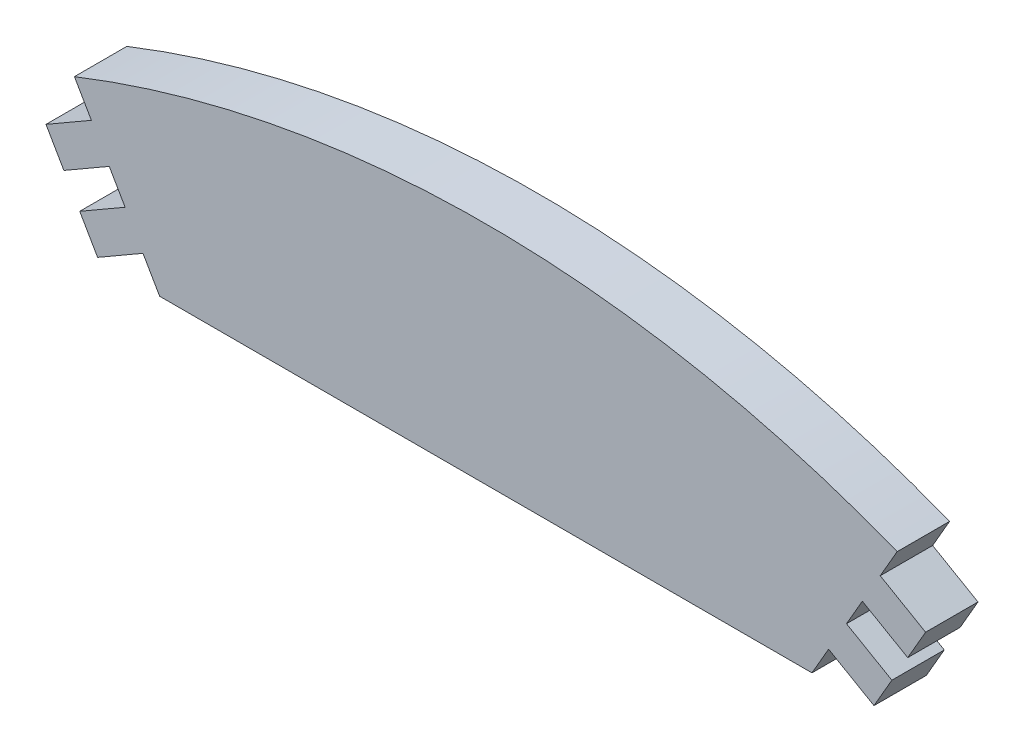
SolidWorks part; units mm, degrees
ref_plane "Front Plane" through (0, 0, 0) normal (0, 0, 1) x (1, 0, 0)
ref_plane "Top Plane" through (0, 0, 0) normal (0, 1, 0) x (1, 0, 0)
ref_plane "Right Plane" through (0, 0, 0) normal (1, 0, 0) x (0, 0, -1)
sketch "Sketch1" plane through (0, 0, 0) normal (0, 0, 1) x (1, 0, 0)
  line L0 (-32.0577, 87.9) -> (32.0577, 87.9)
  line L1 (-32, 88) -> (32, 88) construction
  line L2 (-38.6309, 99.4851) -> (-40.2886, 102.3564) construction
  line L3 (0, 88) -> (0, 136.6413) construction
  line L4 (32.0577, 87.9) -> (33.6943, 90.7347)
  line L5 (32, 88) -> (33.6577, 90.8713) construction
  line L6 (33.6577, 90.8713) -> (38.1178, 88.2963) construction
  line L7 (38.1178, 88.2963) -> (39.7755, 91.1675) construction
  line L8 (39.7755, 91.1675) -> (35.3155, 93.7425) construction
  line L9 (35.3155, 93.7425) -> (36.9732, 96.6138) construction
  line L10 (36.9732, 96.6138) -> (41.4332, 94.0388) construction
  line L11 (41.4332, 94.0388) -> (43.091, 96.9101) construction
  line L12 (43.091, 96.9101) -> (38.6309, 99.4851) construction
  line L13 (38.6309, 99.4851) -> (40.2886, 102.3564) construction
  line L14 (-43.091, 96.9101) -> (-38.6309, 99.4851) construction
  line L15 (-41.4332, 94.0388) -> (-43.091, 96.9101) construction
  line L16 (-36.9732, 96.6138) -> (-41.4332, 94.0388) construction
  line L17 (-35.3155, 93.7425) -> (-36.9732, 96.6138) construction
  line L18 (-39.7755, 91.1675) -> (-35.3155, 93.7425) construction
  line L19 (-38.1178, 88.2963) -> (-39.7755, 91.1675) construction
  line L20 (-33.6577, 90.8713) -> (-38.1178, 88.2963) construction
  line L21 (-32, 88) -> (-33.6577, 90.8713) construction
  line L22 (33.6943, 90.7347) -> (38.1544, 88.1597)
  line L23 (38.1544, 88.1597) -> (39.9121, 91.2041)
  line L24 (39.9121, 91.2041) -> (35.4521, 93.7791)
  line L25 (35.4521, 93.7791) -> (37.0098, 96.4772)
  line L26 (37.0098, 96.4772) -> (41.4698, 93.9022)
  line L27 (41.4698, 93.9022) -> (43.2276, 96.9467)
  line L28 (43.2276, 96.9467) -> (38.7675, 99.5217)
  line L29 (38.7675, 99.5217) -> (40.4333, 102.4068)
  line L30 (-38.7675, 99.5217) -> (-40.4333, 102.4068)
  line L31 (-43.2276, 96.9467) -> (-38.7675, 99.5217)
  line L32 (-41.4698, 93.9022) -> (-43.2276, 96.9467)
  line L33 (-37.0098, 96.4772) -> (-41.4698, 93.9022)
  line L34 (-35.4521, 93.7791) -> (-37.0098, 96.4772)
  line L35 (-39.9121, 91.2041) -> (-35.4521, 93.7791)
  line L36 (-38.1544, 88.1597) -> (-39.9121, 91.2041)
  line L37 (-33.6943, 90.7347) -> (-38.1544, 88.1597)
  line L38 (-32.0577, 87.9) -> (-33.6943, 90.7347)
  arc A0 (-40.2886, 102.3564) -> (40.2886, 102.3564) centre (0, 0) cw construction
  arc A1 (-40.4333, 102.4068) -> (40.4333, 102.4068) centre (0, 0) cw
  point P12 (0, 110)
  dimension "D1" = 110
  dimension "D2" = 22
  dimension "D3" = 120
  dimension "D4" = 64
  dimension "D5" = 5.15
  dimension "D6" = 0.1
extrude "Boss-Extrude1" add sketch "Sketch1" along normal blind 5.15
